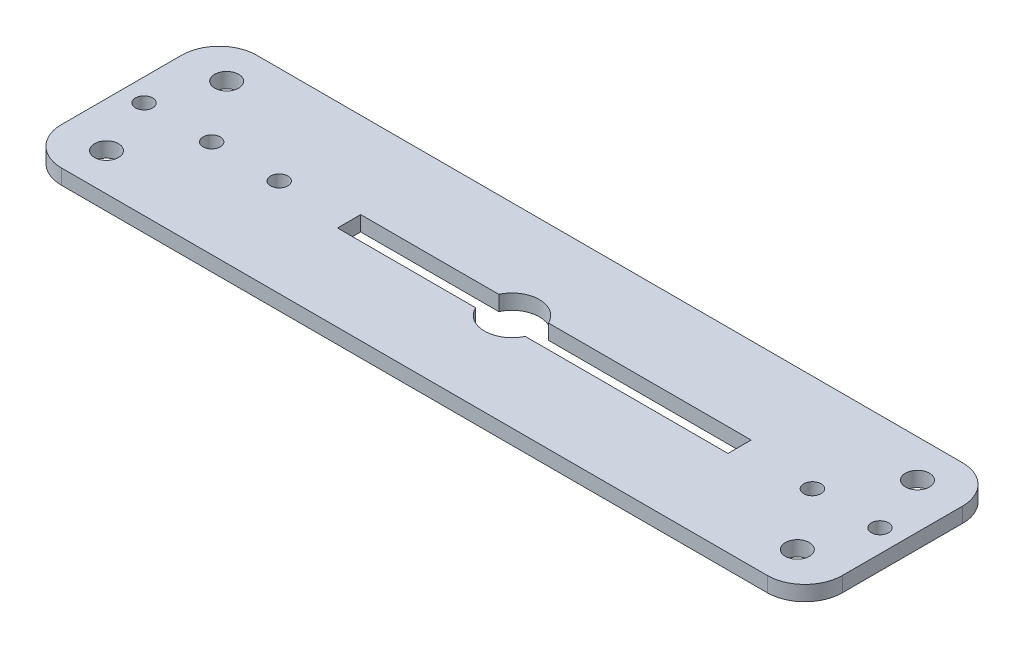
SolidWorks part; units mm, degrees
material "Plástico personalizado"
ref_plane "Plano frontal" through (0, 0, 0) normal (0, 0, 1) x (1, 0, 0)
ref_plane "Plano superior" through (0, 0, 0) normal (0, 1, 0) x (1, 0, 0)
ref_plane "Plano direito" through (0, 0, 0) normal (1, 0, 0) x (0, 0, -1)
sketch "Esboço1" plane through (0, 0, 0) normal (0, 1, 0) x (1, 0, 0)
  line L0 (3.3071, -1.5444) -> (30.3071, -1.5444)
  line L1 (-47, -13) -> (47, -13)
  line L2 (-52, -8) -> (-52, 8)
  line L3 (-47, 13) -> (47, 13)
  line L4 (52, -8) -> (52, 8)
  line L5 (-52, -13) -> (-49.4452, -12.3613) construction
  line L6 (-52, 13) -> (-49.4452, 12.3613) construction
  line L7 (-21.6929, 1.5444) -> (-3.3071, 1.5444)
  line L8 (-21.6929, 1.5444) -> (-21.6929, -1.5444)
  line L9 (-21.6929, -1.5444) -> (-3.3071, -1.5444)
  line L10 (30.3071, 1.5444) -> (30.3071, -1.5444)
  line L13 (49.4452, -12.3613) -> (52, -13) construction
  line L16 (49.4452, 12.3613) -> (52, 13) construction
  line L17 (3.3071, 1.5444) -> (30.3071, 1.5444)
  arc A0 (52, 8) -> (47, 13) centre (47, 8) ccw
  arc A1 (52, -8) -> (47, -13) centre (47, -8) cw
  arc A2 (-47, -13) -> (-52, -8) centre (-47, -8) cw
  arc A3 (-52, 8) -> (-47, 13) centre (-47, 8) cw
  arc A4 (-3.3071, -1.5444) -> (3.3071, -1.5444) centre (0, 0) ccw
  arc A5 (3.3071, 1.5444) -> (-3.3071, 1.5444) centre (0, 0) ccw
  circle A6 centre (46, 8) radius 1.6
  circle A7 centre (46, -8) radius 1.6
  circle A8 centre (49, 0) radius 1.15
  circle A9 centre (40, 0) radius 1.15
  circle A10 centre (-46, 8) radius 1.6
  circle A11 centre (-46, -8) radius 1.6
  circle A12 centre (-40, 0) radius 1.15
  circle A13 centre (-49, 0) radius 1.15
  circle A14 centre (-43, 0) radius 1.15 [skipped]
  circle A15 centre (-31, 0) radius 1.15
  point P0 (0, 0)
  dimension "D3" = 5
  dimension "D4" = 7.3
  dimension "D7" = 6
  dimension "D9" = 3.2
  dimension "D11" = 2.3
  dimension "D15" = 6
  dimension "D16" = 3
  dimension "D17" = 2.3
  dimension "D19" = 9
  dimension "D1" = 104
  dimension "D2" = 26
  dimension "D5" = 52
  dimension "D6" = 27
  dimension "D8" = 5
  dimension "D10" = 5
  dimension "D12" = 9
  dimension "D13" = 3
  dimension "D18" = 9
  dimension "D14" = 2
extrude "Ressalto-extrusão1" add sketch "Esboço1" along normal blind 2
